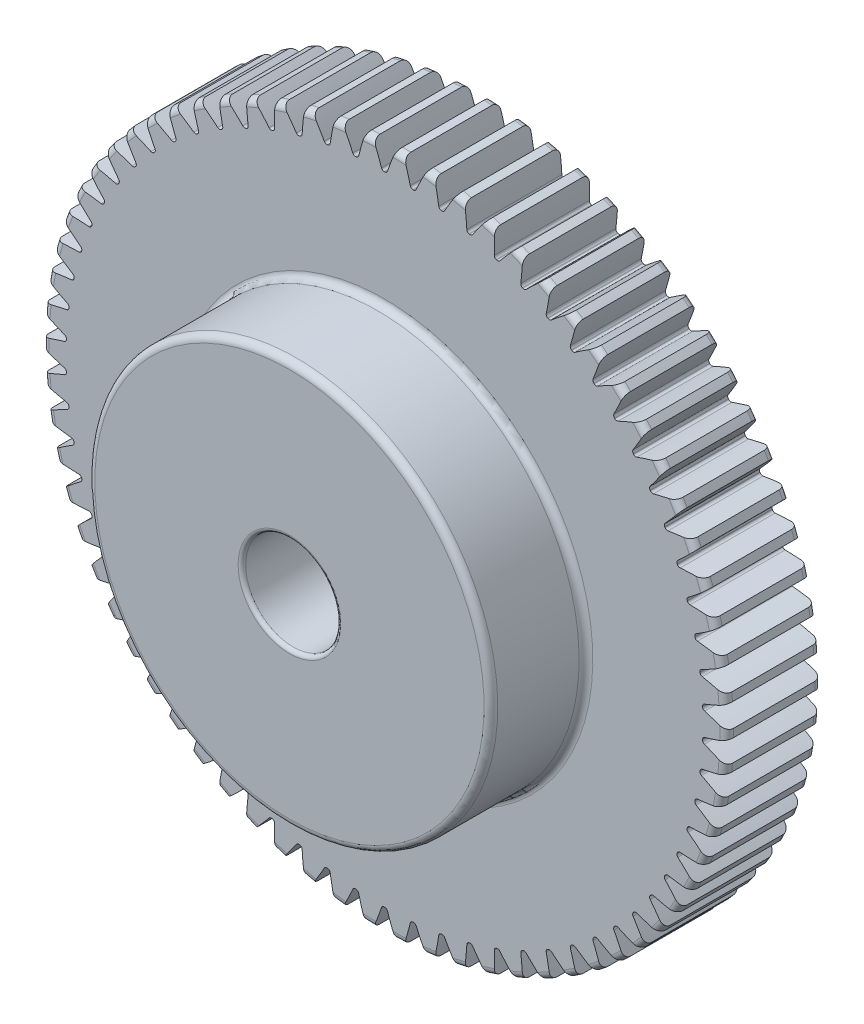
SolidWorks part; units mm, degrees
material "AISI 1020"
ref_plane "Front Plane" through (0, 0, 0) normal (0, 0, 1) x (1, 0, 0)
ref_plane "Top Plane" through (0, 0, 0) normal (0, 1, 0) x (1, 0, 0)
ref_plane "Right Plane" through (0, 0, 0) normal (1, 0, 0) x (0, 0, -1)
sketch "Sketch1" plane through (0, 0, 0) normal (0, 0, 1) x (1, 0, 0)
  line L0 (-889, 0) -> (889, 0) construction
  circle A0 centre (0, 0) radius 45.72 construction
  circle A1 centre (0, 0) radius 44.45 construction
  circle A2 centre (0, 0) radius 42.545 construction
  circle A3 centre (0, 0) radius 26.924 construction
  circle A4 centre (0, 0) radius 6.35 construction
  dimension "D2" = 1.27
  dimension "D3" = 3.175
  dimension "D1" = 3.175
sketch "Sketch2" plane through (0, 0, 0) normal (1, 0, 0) x (0, 0, -1)
  line L0 (0, 0) -> (-12.7, 0) construction
  line L1 (-12.7, 0) -> (-25.4, 0) construction
  dimension "Overall Width" = 25.4
  dimension "Face Width" = 12.7
sketch "Sketch4" plane through (0, 0, 0) normal (1, 0, 0) x (0, 0, -1)
  line L0 (-25.4, 6.35) -> (-25.4, 26.924)
  line L1 (-25.4, 26.924) -> (-12.7, 26.924)
  line L2 (-12.7, 26.924) -> (-12.7, 45.72)
  line L3 (-12.7, 45.72) -> (0, 45.72)
  line L4 (0, 45.72) -> (0, 6.35)
  line L5 (-12.7, 26.924) -> (-12.7, 0) construction
  line L6 (0, 45.72) -> (0, -45.72) construction
  line L7 (-12.7, 26.924) -> (0, 26.924) construction
  line L12 (-25.4, 6.35) -> (0, 6.35)
revolve "Revolve1" add sketch "Sketch4" angle 360 about L1
fillet "Fillet2" radius 0.9144 4 edges at (0, 26.924, 25.4) (0, 26.924, 12.7) (0, 45.72, 12.7) (0, 45.72, 0)
sketch "Sketch7" plane through (0, 0, 12.7) normal (0, 0, 1) x (1, 0, 0)
  line L0 (0, 0) -> (0, 45.72) construction
  line L1 (0.9974, 44.4388) -> (1.4871, 45.6958) construction
  line L3 (2.0512, 45.674) -> (1.9942, 44.4052) construction
  line L4 (1.9942, 44.4052) -> (1.9088, 42.5022) construction
  line L5 (0, 0) -> (1.9088, 42.5022) construction
  line L6 (0.9974, 44.4388) -> (0, 0) construction
  line L7 (0.9974, 44.4388) -> (1.0259, 45.7085) construction
  line L8 (0.9974, 44.4388) -> (0, 0) construction
  circle A0 centre (0, 0) radius 45.72 construction
  arc A1 (-0.0358, 42.545) -> (0.0358, 42.545) centre (0, 0) cw
  circle A2 centre (0, 0) radius 42.545 construction
  arc A3 (-0.9974, 44.4388) -> (0.9974, 44.4388) centre (0, 0) cw construction
  circle A4 centre (0, 0) radius 44.45 construction
  arc A5 (2.5931, 45.6464) -> (1.509, 45.6951) centre (0, 0) ccw construction
  arc A6 (0.9974, 44.4388) -> (2.9901, 44.3493) centre (0, 0) cw construction
  arc A7 (-1.509, 45.6951) -> (1.509, 45.6951) centre (0, 0) cw
  arc A8 (0.3963, 42.8017) -> (1.509, 45.6951) centre (42.4151, 28.3026) cw
  arc A9 (-0.3963, 42.8017) -> (-1.509, 45.6951) centre (-42.4151, 28.3026) ccw
  arc A10 (-0.0358, 42.545) -> (-0.3963, 42.8017) centre (-0.0361, 42.926) cw
  arc A11 (0.0358, 42.545) -> (0.3963, 42.8017) centre (0.0361, 42.926) ccw
  point P26 (-0.3082, 42.5439)
  point P29 (0.3082, 42.5439)
  dimension "D4" = 0.381
  dimension "D5" = 44.45
  dimension "D3" = 20
  dimension "D1" = 3.9898
  dimension "D2" = 1.9949
extrude "Cut-Extrude2" cut sketch "Sketch7" against normal through all
pattern_circular "CirPattern1" count 70 over 360 about axis through (0, 0, 0) along (0, 0, 1) of "Cut-Extrude2"
fillet "Fillet3" radius 0.508 2 edges at (0, 6.35, 0) (0, 6.35, 25.4)
sketch "Sketch8" plane through (0, 0, 0) normal (0, 0, -1) x (-1, 0, 0)
  line L1 (-1.651, 7.7826) -> (1.651, 7.7826)
  line L2 (-1.651, 7.7826) -> (-1.651, 4.4806)
  line L3 (-1.651, 4.4806) -> (1.651, 4.4806)
  line L4 (1.651, 7.7826) -> (1.651, 4.4806)
  circle A1 centre (0, 0) radius 6.35 construction
  point P4 (0, 4.4806)
  point P7 (-1.651, 6.1316)
  dimension "D1" = 3.302
  dimension "D2" = 3.302
extrude "Cut-Extrude3" cut sketch "Sketch8" against normal blind 12.7
equation "\"D1@Sketch1\"=2.5*(\"Pitch Dia.@Sketch1\"/\"Number of Teeth@Sketch1\")"
equation "\"D1@CirPattern1\"=\"Number of Teeth@Sketch1\""
equation "\"D1@Fillet2\"=\"OD@Sketch1\"*.01"
equation "\"D1@Sketch7\"=3.14159*(\"Pitch Dia.@Sketch1\"/\"Number of Teeth@Sketch1\")"
equation "\"D2@Sketch7\"=\"D1@Sketch7\"/2"
equation "\"D4@Sketch7\"=\"D1@Sketch7\"*.0955"
equation "\"D5@Sketch7\"=\"Pitch Dia.@Sketch1\"/2"
